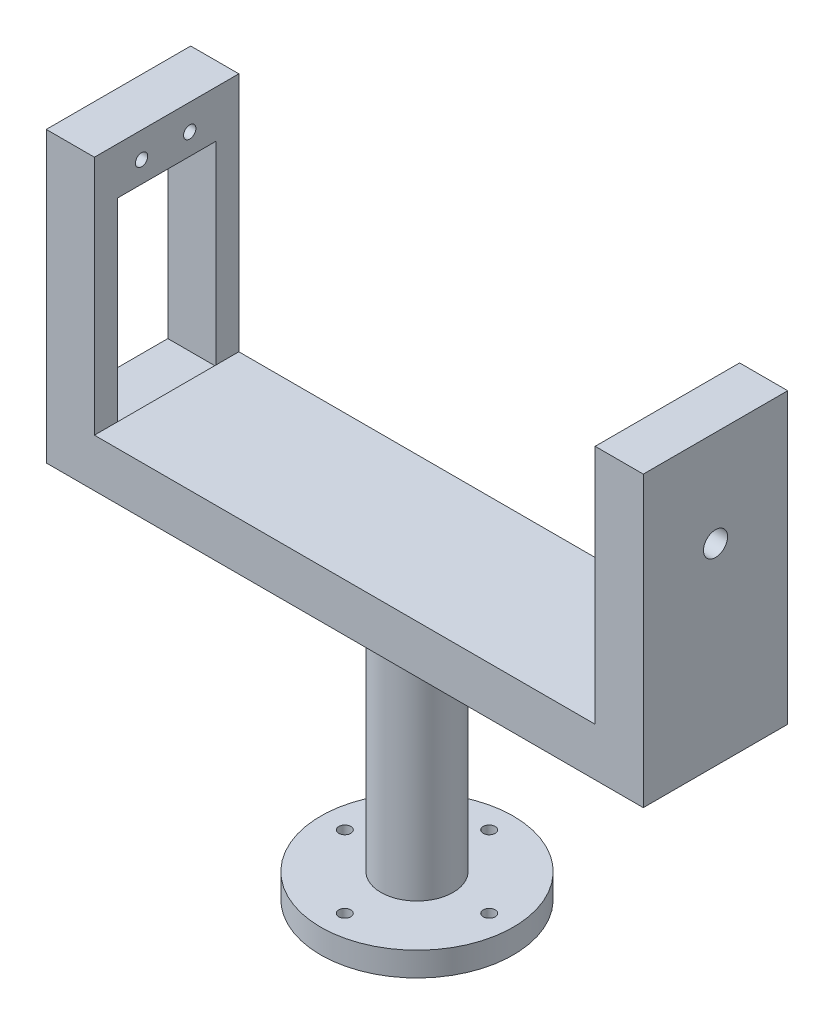
SolidWorks part; units mm, degrees
ref_plane "Front Plane" through (0, 0, 0) normal (0, 0, 1) x (1, 0, 0)
ref_plane "Top Plane" through (0, 0, 0) normal (0, 1, 0) x (1, 0, 0)
ref_plane "Right Plane" through (0, 0, 0) normal (1, 0, 0) x (0, 0, -1)
sketch "Sketch1" plane through (0, 0, 0) normal (0, 0, 1) x (1, 0, 0)
  line L0 (0, 58.7176) -> (0, -38.0262) construction
  line L1 (-52, 50) -> (-52, 0)
  line L2 (-52, 0) -> (52, 0)
  line L3 (52, 0) -> (52, 50)
  line L4 (52, 50) -> (62, 50)
  line L5 (62, 50) -> (62, -10)
  line L6 (62, -10) -> (-62, -10)
  line L7 (-62, -10) -> (-62, 50)
  line L8 (-62, 50) -> (-52, 50)
  dimension "D1" = 60
  dimension "D2" = 10
  dimension "D3" = 10
  dimension "D4" = 10
  dimension "D5" = 52
  dimension "D6" = 52
extrude "Boss-Extrude1" add sketch "Sketch1" along normal mid plane 30
sketch "Sketch3" plane through (0, -10, 0) normal (0, -1, 0) x (1, 0, 0)
  circle A0 centre (0, 0) radius 7.5
  dimension "D1" = 15
extrude "Boss-Extrude2" add sketch "Sketch3" along normal blind 50
sketch "Sketch4" plane through (0, -60, 0) normal (0, -1, 0) x (1, 0, 0)
  line L0 (0, 37.0495) -> (0, -39.8232) construction
  line L1 (-31.7001, 0) -> (28.9263, 0) construction
  circle A0 centre (0, 0) radius 20
  circle A1 centre (0, 15) radius 1.25
  circle A2 centre (-15, 0) radius 1.25
  circle A3 centre (15, 0) radius 1.25
  circle A4 centre (0, -15) radius 1.25
  dimension "D1" = 40
  dimension "D2" = 2.5
  dimension "D3" = 15
  dimension "D4" = 15
extrude "Boss-Extrude3" add sketch "Sketch4" along normal blind 5
sketch "Sketch5" plane through (-62, 0, 0) normal (-1, 0, 0) x (0, 0, 1)
  line L1 (-10.25, -0.25) -> (10.25, -0.25)
  line L2 (-10.25, -0.25) -> (-10.25, 40.25)
  line L3 (-10.25, 40.25) -> (10.25, 40.25)
  line L4 (10.25, -0.25) -> (10.25, 40.25)
  line L5 (-10.25, -0.25) -> (10.25, 40.25) construction
  line L6 (-10.25, 40.25) -> (10.25, -0.25) construction
  line L7 (15, -10) -> (-15, -10) construction
  line L8 (15, 50) -> (-15, 50) construction
  line L9 (0, 51.7138) -> (0, -10.949) construction
  line L10 (-21.4247, 20) -> (19.1163, 20) construction
  line L11 (-15, 50) -> (-15, -10) construction
  line L12 (15, 50) -> (15, -10) construction
  circle A4 centre (-4.8, 44.65) radius 1.28
  circle A5 centre (5.2, 44.65) radius 1.28
  circle A6 centre (-4.8, -4.5375) radius 1.28
  circle A7 centre (5.2, -4.5375) radius 1.28
  point P0 (0, 20)
  point P22 (0, 0)
  point P23 (0, 0)
  point P24 (0, 0)
  point P25 (0, 0)
  point P26 (0, 0)
  dimension "D5" = 10.2
  dimension "D4" = 2.56
  dimension "D1" = 20.5
  dimension "D2" = 9.75
  dimension "D3" = 9.75
  dimension "D6" = 5.35
  dimension "D7" = 9.8
extrude "Cut-Extrude1" cut sketch "Sketch5" against normal blind 10
sketch "Sketch7" plane through (62, 0, 0) normal (1, 0, 0) x (0, 0, -1)
  circle A0 centre (0, 30) radius 2.5
  circle A1 centre (-5.2, 44.65) radius 1.28 construction
  dimension "D1" = 5
  dimension "D2" = 14.65
extrude "Cut-Extrude2" cut sketch "Sketch7" against normal blind 10
